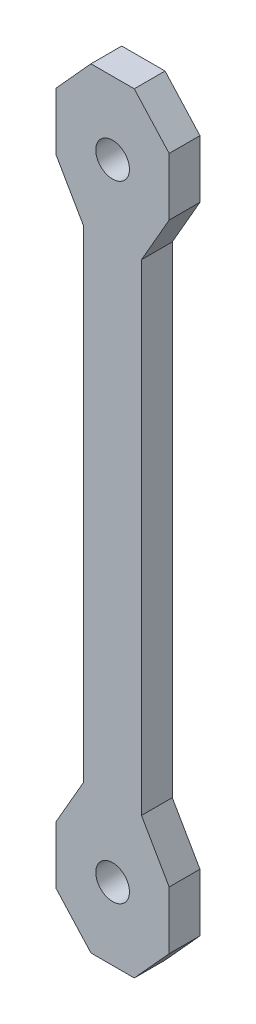
SolidWorks part; units mm, degrees
material "3.1655 (EN AW-2011)"
ref_plane "Alzado" through (0, 0, 0) normal (0, 0, 1) x (1, 0, 0)
ref_plane "Planta" through (0, 0, 0) normal (0, 1, 0) x (1, 0, 0)
ref_plane "Vista lateral" through (0, 0, 0) normal (1, 0, 0) x (0, 0, -1)
sketch "Croquis1" plane through (0, 0, 0) normal (0, 0, 1) x (1, 0, 0)
  line L0 (-6, 15.1492) -> (-6, -34.8508)
  line L1 (6, 15.1492) -> (6, -34.8508)
  line L2 (-6, -34.8508) -> (-11.75, -44.8508)
  line L3 (-11.75, -44.8508) -> (-11.75, -56.8508)
  line L4 (-11.75, -56.8508) -> (-4.5, -64.8508)
  line L5 (-4.5, -64.8508) -> (4.5, -64.8508)
  line L6 (4.5, -64.8508) -> (11.75, -56.8508)
  line L7 (11.75, -56.8508) -> (11.75, -44.8508)
  line L8 (11.75, -44.8508) -> (6, -34.8508)
  line L9 (-6, 15.1492) -> (6, 15.1492) construction
  line L10 (11.75, 75.1492) -> (6, 65.1492)
  line L11 (11.75, 87.1492) -> (11.75, 75.1492)
  line L12 (4.5, 95.1492) -> (11.75, 87.1492)
  line L13 (-4.5, 95.1492) -> (4.5, 95.1492)
  line L14 (-11.75, 87.1492) -> (-4.5, 95.1492)
  line L15 (-11.75, 75.1492) -> (-11.75, 87.1492)
  line L16 (-6, 65.1492) -> (-11.75, 75.1492)
  line L17 (-6, 15.1492) -> (-6, 65.1492)
  line L18 (6, 65.1492) -> (6, 15.1492)
  circle A0 centre (0, -49.8508) radius 3.5
  circle A1 centre (0, 80.1492) radius 3.5
  dimension "D15" = 7
  dimension "D1" = 12
  dimension "D2" = 6
  dimension "D3" = 30
  dimension "D4" = 8
  dimension "D5" = 8
  dimension "D6" = 12
  dimension "D7" = 12
  dimension "D8" = 5.75
  dimension "D9" = 5.75
  dimension "D10" = 9
  dimension "D11" = 7.25
  dimension "D12" = 30
  dimension "D13" = 50
  dimension "D14" = 50
  dimension "D16" = 65
extrude "Saliente-Extruir1" add sketch "Croquis1" along normal blind 6.4
